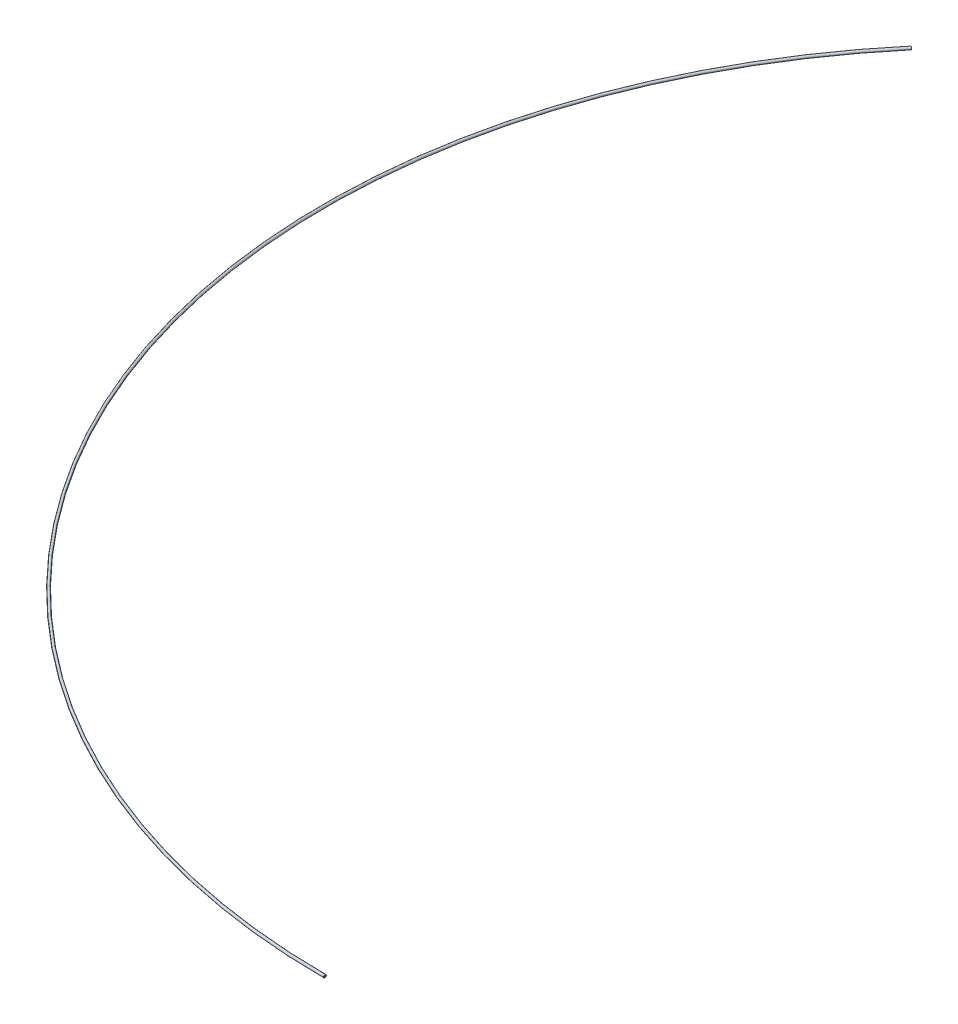
SolidWorks part; units mm, degrees
material "Hexcel AS4C (3000 Filaments)"
ref_plane "Front Plane" through (0, 0, 0) normal (0, 0, 1) x (1, 0, 0)
ref_plane "Top Plane" through (0, 0, 0) normal (0, 1, 0) x (1, 0, 0)
ref_plane "Right Plane" through (0, 0, 0) normal (1, 0, 0) x (0, 0, -1)
sketch "Sketch1" plane through (0, 0, 0) normal (0, 1, 0) x (1, 0, 0)
  line L0 (337.5, 0) -> (-337.5, 0) construction
  line L1 (0, 0) -> (0, -724.8569) construction
  line L2 (0, -724.8569) -> (103.1818, -724.8569) construction
  arc A0 (0, -724.8569) -> (-337.5, 0) centre (0, -283.8569) cw
  point P4 (0, 0)
  dimension "D2" = 441
  dimension "D1" = 675
sketch "Sketch2" plane through (0, 0, 0) normal (1, 0, 0) x (0, 0, -1)
  line L0 (-724, 0) -> (0, 0) construction
  circle A2 centre (-724, 0) radius 0.9
  circle A3 centre (-724, 0) radius 0.5
  dimension "D1" = 1.8
  dimension "D2" = 1
  dimension "D3" = 724
sweep "Sweep1" add profiles "Sketch2" path "Sketch1"
